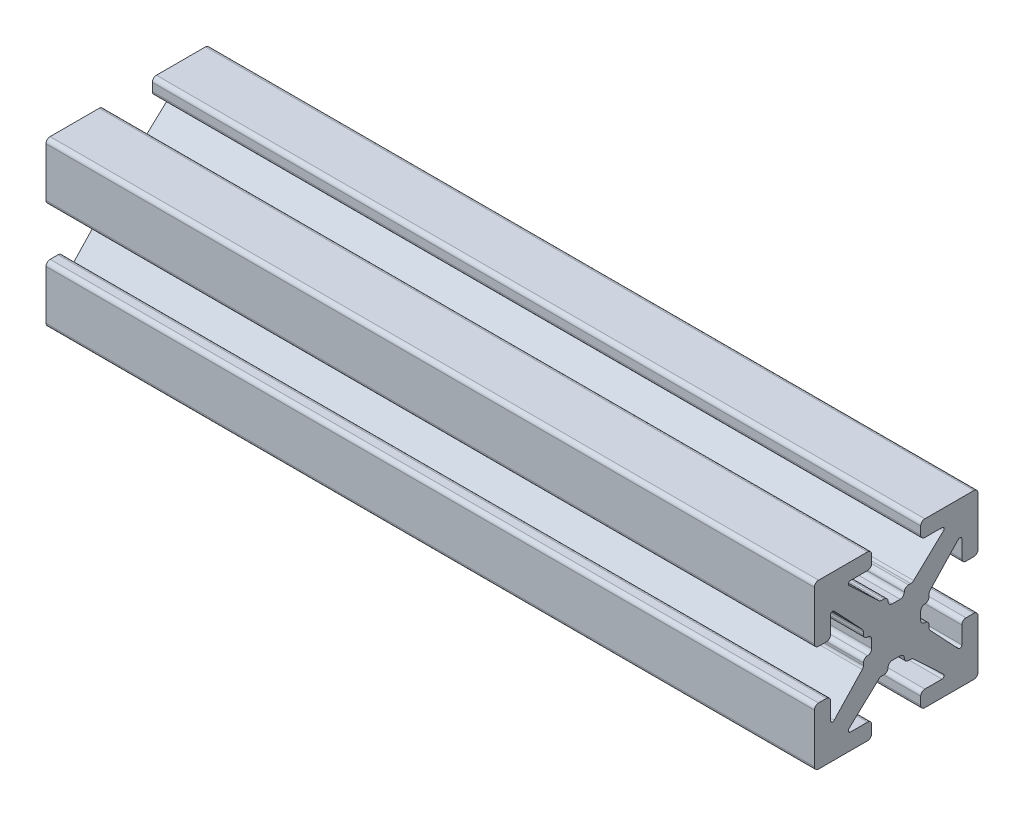
SolidWorks part; units mm, degrees
ref_plane "Front Plane" through (0, 0, 0) normal (0, 0, 1) x (1, 0, 0)
ref_plane "Top Plane" through (0, 0, 0) normal (0, 1, 0) x (1, 0, 0)
ref_plane "Right Plane" through (0, 0, 0) normal (1, 0, 0) x (0, 0, -1)
sketch "Sketch1" plane through (0, 0, 0) normal (1, 0, 0) x (0, 0, -1)
  line L0 (0, 0) -> (0, 1.4986) construction
  line L1 (-0.2413, 1.4986) -> (0.2413, 1.4986)
  line L2 (5.0038, 1.7526) -> (5.0038, 4.7498)
  line L3 (0.7493, 2.0066) -> (0.8899, 2.0066)
  line L4 (1.0639, 2.0756) -> (2.8908, 3.7937)
  line L5 (2.8038, 4.0132) -> (1.7526, 4.0132)
  line L6 (1.4986, 4.2672) -> (1.4986, 4.7498)
  line L7 (1.7526, 5.0038) -> (4.7498, 5.0038)
  line L8 (5.0038, 5.0038) -> (0, 0) construction
  line L9 (0, 0) -> (8.6271, 0) construction
  line L10 (0, 0) -> (0, 5.0038) construction
  line L11 (4.2672, 1.4986) -> (4.7498, 1.4986)
  line L12 (4.0132, 2.8038) -> (4.0132, 1.7526)
  line L13 (2.0756, 1.0639) -> (3.7937, 2.8908)
  line L14 (2.0066, 0.7493) -> (2.0066, 0.8899)
  line L15 (1.4986, -0.2413) -> (1.4986, 0.2413)
  line L16 (0, 0) -> (1.4986, 0) construction
  line L17 (-0.2413, -1.4986) -> (0.2413, -1.4986)
  line L18 (0.7493, -2.0066) -> (0.8899, -2.0066)
  line L19 (1.0639, -2.0756) -> (2.8908, -3.7937)
  line L20 (2.8038, -4.0132) -> (1.7526, -4.0132)
  line L21 (1.4986, -4.2672) -> (1.4986, -4.7498)
  line L22 (1.7526, -5.0038) -> (4.7498, -5.0038)
  line L23 (5.0038, -1.7526) -> (5.0038, -4.7498)
  line L24 (4.2672, -1.4986) -> (4.7498, -1.4986)
  line L25 (4.0132, -2.8038) -> (4.0132, -1.7526)
  line L26 (2.0756, -1.0639) -> (3.7937, -2.8908)
  line L27 (2.0066, -0.7493) -> (2.0066, -0.8899)
  line L28 (-0.7493, 2.0066) -> (-0.8899, 2.0066)
  line L29 (-1.0639, 2.0756) -> (-2.8908, 3.7937)
  line L30 (-2.8038, 4.0132) -> (-1.7526, 4.0132)
  line L31 (-1.4986, 4.2672) -> (-1.4986, 4.7498)
  line L32 (-1.7526, 5.0038) -> (-4.7498, 5.0038)
  line L33 (-5.0038, 1.7526) -> (-5.0038, 4.7498)
  line L34 (-4.2672, 1.4986) -> (-4.7498, 1.4986)
  line L35 (-4.0132, 2.8038) -> (-4.0132, 1.7526)
  line L36 (-2.0756, 1.0639) -> (-3.7937, 2.8908)
  line L37 (-2.0066, 0.7493) -> (-2.0066, 0.8899)
  line L38 (-1.4986, -0.2413) -> (-1.4986, 0.2413)
  line L39 (-2.0066, -0.7493) -> (-2.0066, -0.8899)
  line L40 (-2.0756, -1.0639) -> (-3.7937, -2.8908)
  line L41 (-4.0132, -2.8038) -> (-4.0132, -1.7526)
  line L42 (-4.2672, -1.4986) -> (-4.7498, -1.4986)
  line L43 (-5.0038, -1.7526) -> (-5.0038, -4.7498)
  line L44 (-1.7526, -5.0038) -> (-4.7498, -5.0038)
  line L45 (-1.4986, -4.2672) -> (-1.4986, -4.7498)
  line L46 (-2.8038, -4.0132) -> (-1.7526, -4.0132)
  line L47 (-1.0639, -2.0756) -> (-2.8908, -3.7937)
  line L48 (-0.7493, -2.0066) -> (-0.8899, -2.0066)
  arc A0 (2.8908, 3.7937) -> (2.8038, 4.0132) centre (2.8038, 3.8862) ccw
  arc A1 (0.4953, 1.7526) -> (0.7493, 2.0066) centre (0.7493, 1.7526) cw
  arc A2 (0.8899, 2.0066) -> (1.0639, 2.0756) centre (0.8899, 2.2606) ccw
  arc A3 (1.7526, 4.0132) -> (1.4986, 4.2672) centre (1.7526, 4.2672) cw
  arc A4 (1.4986, 4.7498) -> (1.7526, 5.0038) centre (1.7526, 4.7498) cw
  arc A5 (0.2413, 1.4986) -> (0.4953, 1.7526) centre (0.2413, 1.7526) ccw
  arc A6 (4.7498, 1.4986) -> (5.0038, 1.7526) centre (4.7498, 1.7526) ccw
  arc A7 (4.0132, 1.7526) -> (4.2672, 1.4986) centre (4.2672, 1.7526) ccw
  arc A8 (3.7937, 2.8908) -> (4.0132, 2.8038) centre (3.8862, 2.8038) cw
  arc A9 (2.0066, 0.8899) -> (2.0756, 1.0639) centre (2.2606, 0.8899) cw
  arc A10 (1.7526, 0.4953) -> (2.0066, 0.7493) centre (1.7526, 0.7493) ccw
  arc A11 (1.4986, 0.2413) -> (1.7526, 0.4953) centre (1.7526, 0.2413) cw
  arc A12 (0.2413, -1.4986) -> (0.4953, -1.7526) centre (0.2413, -1.7526) cw
  arc A13 (0.4953, -1.7526) -> (0.7493, -2.0066) centre (0.7493, -1.7526) ccw
  arc A14 (0.8899, -2.0066) -> (1.0639, -2.0756) centre (0.8899, -2.2606) cw
  arc A15 (2.8908, -3.7937) -> (2.8038, -4.0132) centre (2.8038, -3.8862) cw
  arc A16 (1.7526, -4.0132) -> (1.4986, -4.2672) centre (1.7526, -4.2672) ccw
  arc A17 (1.4986, -4.7498) -> (1.7526, -5.0038) centre (1.7526, -4.7498) ccw
  arc A18 (4.7498, -1.4986) -> (5.0038, -1.7526) centre (4.7498, -1.7526) cw
  arc A19 (4.0132, -1.7526) -> (4.2672, -1.4986) centre (4.2672, -1.7526) cw
  arc A20 (3.7937, -2.8908) -> (4.0132, -2.8038) centre (3.8862, -2.8038) ccw
  arc A21 (2.0066, -0.8899) -> (2.0756, -1.0639) centre (2.2606, -0.8899) ccw
  arc A22 (1.7526, -0.4953) -> (2.0066, -0.7493) centre (1.7526, -0.7493) cw
  arc A23 (1.4986, -0.2413) -> (1.7526, -0.4953) centre (1.7526, -0.2413) ccw
  arc A24 (-0.2413, 1.4986) -> (-0.4953, 1.7526) centre (-0.2413, 1.7526) cw
  arc A25 (-0.4953, 1.7526) -> (-0.7493, 2.0066) centre (-0.7493, 1.7526) ccw
  arc A26 (-0.8899, 2.0066) -> (-1.0639, 2.0756) centre (-0.8899, 2.2606) cw
  arc A27 (-2.8908, 3.7937) -> (-2.8038, 4.0132) centre (-2.8038, 3.8862) cw
  arc A28 (-1.7526, 4.0132) -> (-1.4986, 4.2672) centre (-1.7526, 4.2672) ccw
  arc A29 (-1.4986, 4.7498) -> (-1.7526, 5.0038) centre (-1.7526, 4.7498) ccw
  arc A30 (-4.7498, 1.4986) -> (-5.0038, 1.7526) centre (-4.7498, 1.7526) cw
  arc A31 (-4.0132, 1.7526) -> (-4.2672, 1.4986) centre (-4.2672, 1.7526) cw
  arc A32 (-3.7937, 2.8908) -> (-4.0132, 2.8038) centre (-3.8862, 2.8038) ccw
  arc A33 (-2.0066, 0.8899) -> (-2.0756, 1.0639) centre (-2.2606, 0.8899) ccw
  arc A34 (-1.7526, 0.4953) -> (-2.0066, 0.7493) centre (-1.7526, 0.7493) cw
  arc A35 (-1.4986, 0.2413) -> (-1.7526, 0.4953) centre (-1.7526, 0.2413) ccw
  arc A36 (-1.4986, -0.2413) -> (-1.7526, -0.4953) centre (-1.7526, -0.2413) cw
  arc A37 (-1.7526, -0.4953) -> (-2.0066, -0.7493) centre (-1.7526, -0.7493) ccw
  arc A38 (-2.0066, -0.8899) -> (-2.0756, -1.0639) centre (-2.2606, -0.8899) cw
  arc A39 (-3.7937, -2.8908) -> (-4.0132, -2.8038) centre (-3.8862, -2.8038) cw
  arc A40 (-4.0132, -1.7526) -> (-4.2672, -1.4986) centre (-4.2672, -1.7526) ccw
  arc A41 (-4.7498, -1.4986) -> (-5.0038, -1.7526) centre (-4.7498, -1.7526) ccw
  arc A42 (-1.4986, -4.7498) -> (-1.7526, -5.0038) centre (-1.7526, -4.7498) cw
  arc A43 (-1.7526, -4.0132) -> (-1.4986, -4.2672) centre (-1.7526, -4.2672) cw
  arc A44 (-2.8908, -3.7937) -> (-2.8038, -4.0132) centre (-2.8038, -3.8862) ccw
  arc A45 (-0.8899, -2.0066) -> (-1.0639, -2.0756) centre (-0.8899, -2.2606) ccw
  arc A46 (-0.4953, -1.7526) -> (-0.7493, -2.0066) centre (-0.7493, -1.7526) cw
  arc A47 (-0.2413, -1.4986) -> (-0.4953, -1.7526) centre (-0.2413, -1.7526) ccw
  arc A48 (-4.7498, 5.0038) -> (-5.0038, 4.7498) centre (-4.7498, 4.7498) ccw
  arc A49 (-5.0038, -4.7498) -> (-4.7498, -5.0038) centre (-4.7498, -4.7498) ccw
  arc A50 (4.7498, -5.0038) -> (5.0038, -4.7498) centre (4.7498, -4.7498) ccw
  arc A51 (4.7498, 5.0038) -> (5.0038, 4.7498) centre (4.7498, 4.7498) cw
  point P14 (3.1242, 4.0132)
  point P19 (0.9906, 2.0066)
  point P150 (0, -1.4986)
  point P152 (-5.0038, 5.0038)
  point P155 (-5.0038, -5.0038)
  point P158 (5.0038, -5.0038)
  dimension "D10" = 0.127
  dimension "D11" = 0.254
  dimension "D2" = 0.254
  dimension "D1" = 10.0076
  dimension "D3" = 2.9972
  dimension "D4" = 0.508
  dimension "D5" = 2.9972
  dimension "D6" = 0.9906
  dimension "D7" = 1.6256
  dimension "D8" = 1.9812
  dimension "D9" = 0.9906
extrude "Boss.-Extru.1" add sketch "Sketch1" along normal blind 47
